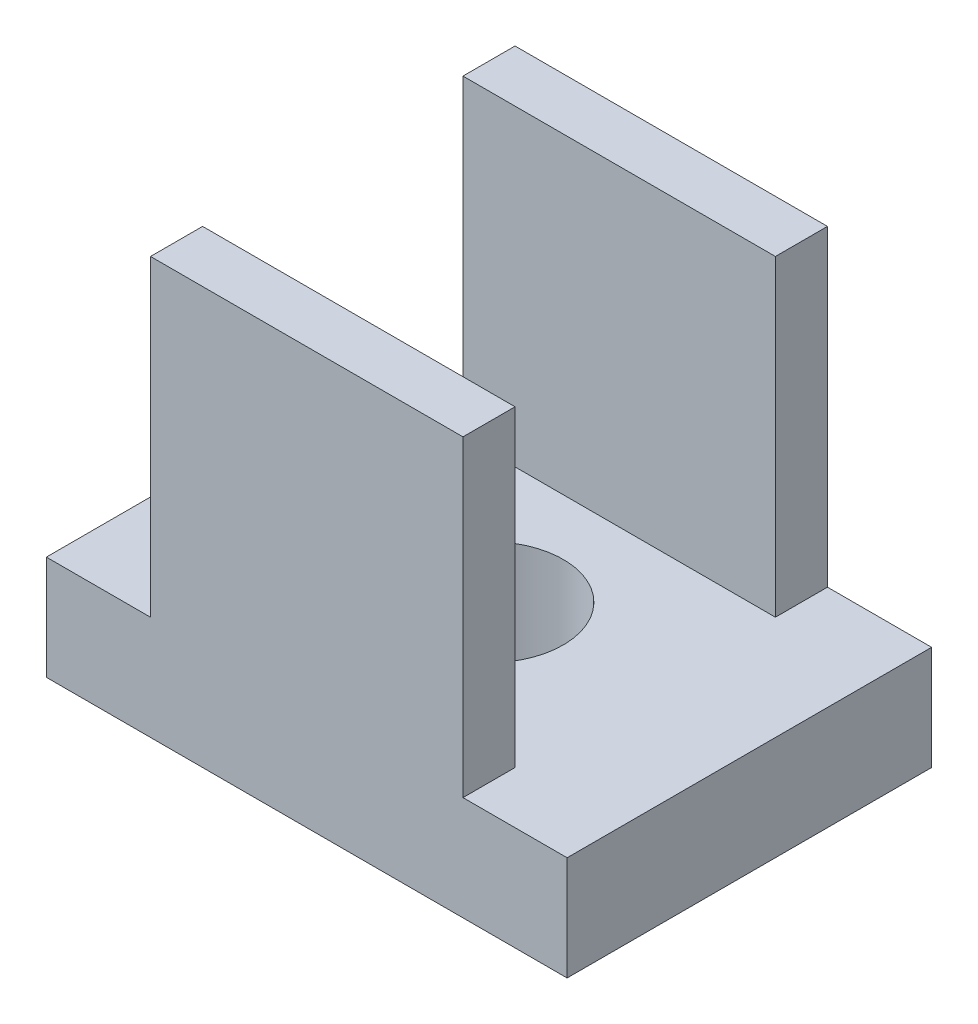
SolidWorks part; units mm, degrees
ref_plane "Front Plane" through (0, 0, 0) normal (0, 0, 1) x (1, 0, 0)
ref_plane "Top Plane" through (0, 0, 0) normal (0, 1, 0) x (1, 0, 0)
ref_plane "Right Plane" through (0, 0, 0) normal (1, 0, 0) x (0, 0, -1)
sketch "Sketch1" plane through (0, 0, 0) normal (0, 1, 0) x (1, 0, 0)
  line L1 (-5, -3.5) -> (5, -3.5)
  line L2 (-5, -3.5) -> (-5, 3.5)
  line L3 (-5, 3.5) -> (5, 3.5)
  line L4 (5, -3.5) -> (5, 3.5)
  line L5 (-5, -3.5) -> (5, 3.5) construction
  line L6 (-5, 3.5) -> (5, -3.5) construction
  point P0 (0, 0)
  dimension "D1" = 10
  dimension "D2" = 7
extrude "Boss-Extrude1" add sketch "Sketch1" along normal blind 2
sketch "Sketch2" plane through (0, 2, 0) normal (0, 1, 0) x (1, 0, 0)
  circle A0 centre (0, 0) radius 1.425
  dimension "D1" = 2.85
extrude "Cut-Extrude1" cut sketch "Sketch2" against normal blind 2
sketch "Sketch3" plane through (0, 2, 0) normal (0, 1, 0) x (1, 0, 0)
  line L0 (5, 3.5) -> (-5, 3.5) construction
  line L1 (-3, 3.5) -> (3, 3.5)
  line L2 (-3, 3.5) -> (-3, 2.5)
  line L3 (-3, 2.5) -> (3, 2.5)
  line L4 (3, 3.5) -> (3, 2.5)
  line L5 (-5, -3.5) -> (5, -3.5) construction
  line L6 (-3, -3.5) -> (3, -3.5)
  line L7 (-3, -3.5) -> (-3, -2.5)
  line L8 (-3, -2.5) -> (3, -2.5)
  line L9 (3, -3.5) -> (3, -2.5)
  line L10 (0, 0) -> (0, 7.7248) construction
  line L11 (0, 7.7248) -> (0, 0) construction
  line L12 (0, 0) -> (7.1888, 0) construction
  dimension "D1" = 6
  dimension "D2" = 1
extrude "Boss-Extrude2" add sketch "Sketch3" along normal blind 6
